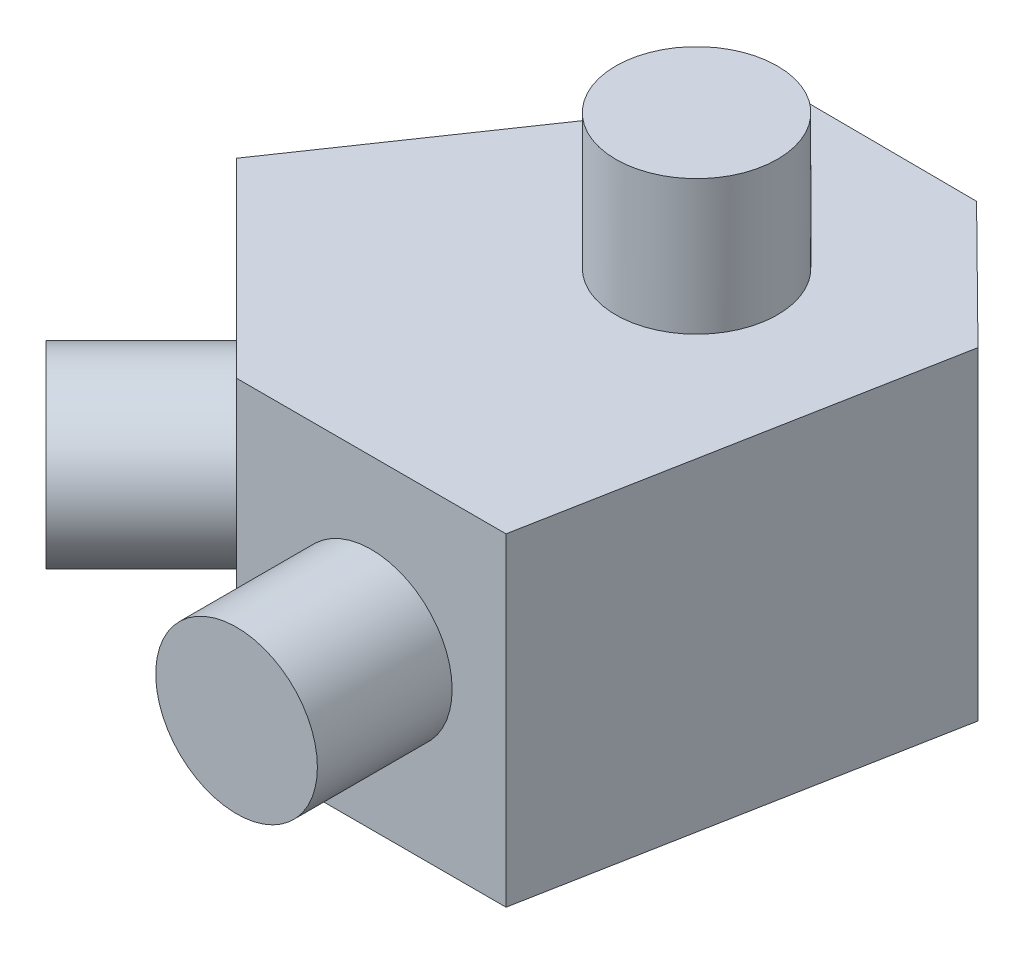
SolidWorks part; units mm, degrees
ref_plane "Front Plane" through (0, 0, 0) normal (0, 0, 1) x (1, 0, 0)
ref_plane "Top Plane" through (0, 0, 0) normal (0, 1, 0) x (1, 0, 0)
ref_plane "Right Plane" through (0, 0, 0) normal (1, 0, 0) x (0, 0, -1)
sketch "Sketch1" plane through (0, 0, 0) normal (0, 1, 0) x (1, 0, 0)
  line L0 (-8.9803, 8.9803) -> (0, 0)
  line L1 (0, 0) -> (12.7, 0)
  line L2 (-8.9803, 8.9803) -> (1.7691, 24.7077)
  line L3 (1.7691, 24.7077) -> (10.2143, 24.6596)
  line L4 (10.2143, 24.6596) -> (16.2201, 18.722)
  line L5 (16.2201, 18.722) -> (12.7, 0)
  line L6 (0, 0) -> (15.9814, 38.5826) construction
  dimension "D1" = 135
  dimension "D2" = 12.7
  dimension "D3" = 12.7
  dimension "D4" = 67.5
  dimension "D5" = 8.4454
  dimension "D6" = 8.4454
  dimension "D7" = 19.05
  dimension "D8" = 19.05
extrude "Boss-Extrude1" add sketch "Sketch1" along normal blind 15.24
sketch "Sketch2" plane through (0, 0, 0) normal (0, 0, 1) x (1, 0, 0)
  line L0 (0, 7.62) -> (15.0157, 7.62) construction
  line L1 (0, 15.24) -> (0, 0) construction
  line L2 (6.35, 15.24) -> (6.35, -2.2419) construction
  line L3 (0, 15.24) -> (12.7, 15.24) construction
  circle A0 centre (6.35, 7.62) radius 3.81
  point P8 (6.35, 7.62)
extrude "Boss-Extrude2" add sketch "Sketch2" along normal blind 6.35 contours A0
sketch "Sketch3" plane through (0, 15.24, 0) normal (0, 1, 0) x (1, 0, 0)
  line L0 (0, 0) -> (10.2143, 24.6596) construction
ref_plane "Plane1" through (0, 0, 0) normal (0.9239, 0, 0.3827) x (0.3827, 0, -0.9239)
mirror "Mirror1" about plane through (0, 0, 0) normal (0.9239, 0, 0.3827) of "Boss-Extrude2"
sketch "Sketch5" plane through (0, 15.24, 0) normal (0, 1, 0) x (1, 0, 0)
  line L0 (6.35, 0) -> (6.35, 28.1321) construction
  line L1 (2.54, 0) -> (10.16, 0) construction
  line L2 (-4.4901, 4.4901) -> (16.6739, 25.6542) construction
  line L3 (-8.9803, 8.9803) -> (0, 0) construction
  circle A0 centre (6.35, 15.3303) radius 3.81
  point P8 (6.35, 15.3303)
  dimension "D1" = 7.62
  dimension "D2" = 16.5933
extrude "Boss-Extrude3" add sketch "Sketch5" along normal blind 6.35
equation "\"H\"=0.332495"
equation "\"D5@Sketch1\"=\"H\""
equation "\"w\"=0.75"
equation "\"D7@Sketch1\"=\"w\""
equation "\"D6@Sketch1\"=\"H\""
equation "\"D8@Sketch1\"=\"w\""
